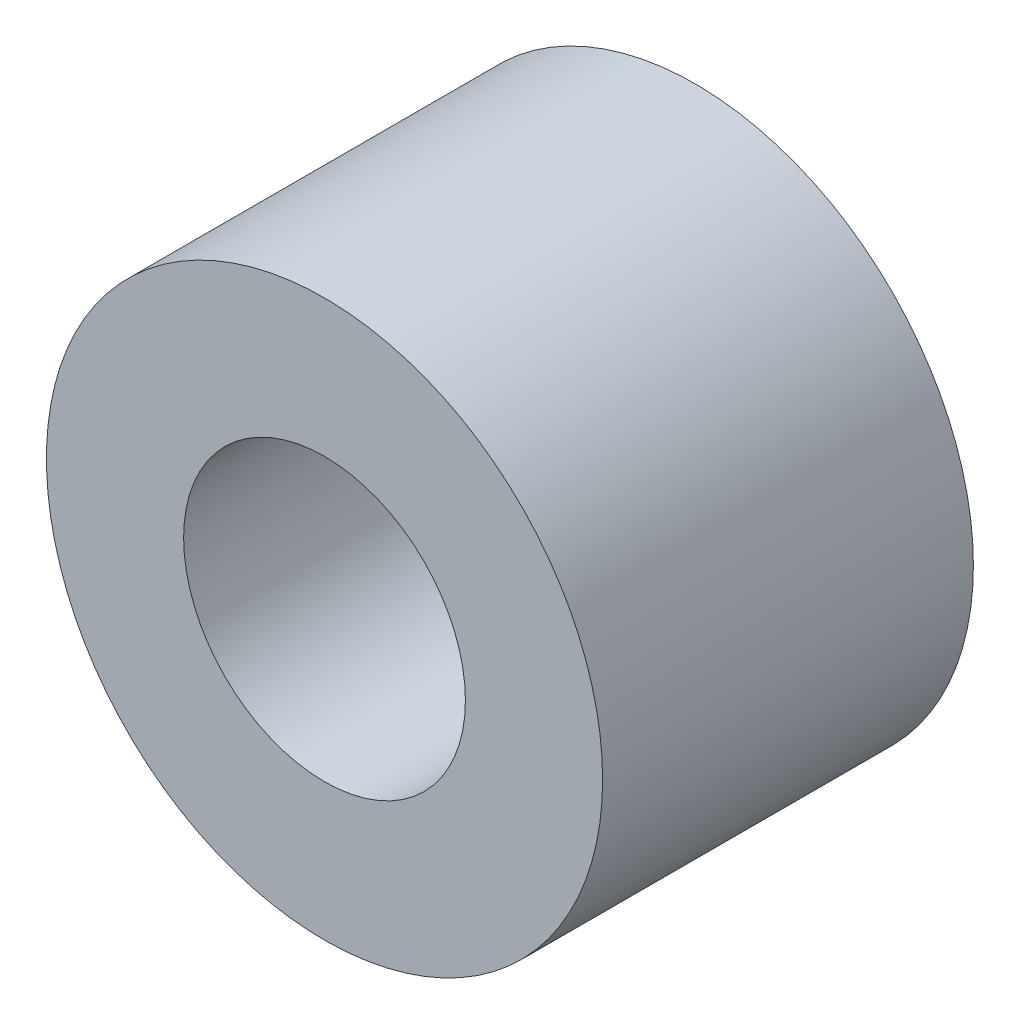
SolidWorks part; units mm, degrees
ref_plane "Front Plane" through (0, 0, 0) normal (0, 0, 1) x (1, 0, 0)
ref_plane "Top Plane" through (0, 0, 0) normal (0, 1, 0) x (1, 0, 0)
ref_plane "Right Plane" through (0, 0, 0) normal (1, 0, 0) x (0, 0, -1)
sketch "Sketch1" plane through (0, 0, 0) normal (0, 0, 1) x (1, 0, 0)
  line L0 (0, 4.826) -> (0, 9.525) construction
  line L1 (0, -4.826) -> (0, -9.525) construction
  circle A0 centre (0, 0) radius 9.525
  circle A1 centre (0, 0) radius 4.826
  dimension "OD" = 19.05
  dimension "ID" = 9.652
sketch "Sketch2" plane through (0, 0, 0) normal (1, 0, 0) x (0, 0, -1)
  line L0 (-6.35, 4.826) -> (6.35, 4.826) construction
  line L1 (-6.35, -4.826) -> (6.35, -4.826) construction
  line L2 (-6.35, -9.525) -> (6.35, -9.525) construction
  line L3 (-6.35, 9.525) -> (6.35, 9.525) construction
  dimension "Length" = 12.7
extrude "Extrude1" add sketch "Sketch1" along normal up to vertex (6.35 mm away) and the other way up to vertex (6.35 mm away) up to point (0, 4.826, 6.35) other way up to point (0, 4.826, -6.35)
sketch "Sketch3" plane through (0, 0, 6.35) normal (0, 0, 1) x (1, 0, 0)
  circle A0 centre (0, 0) radius 4.826 construction
  circle A3 centre (0, 0) radius 4.826
  point P3 (-4.826, 0)
